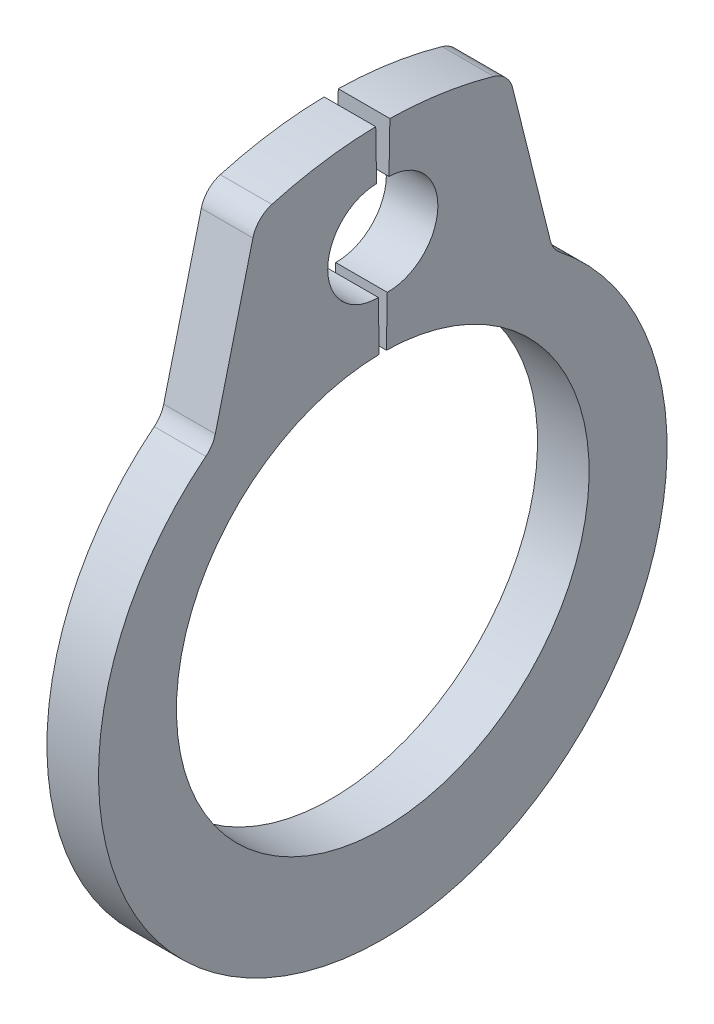
SolidWorks part; units mm, degrees
material "Cast Carbon Steel"
ref_plane "Front" through (0, 0, 0) normal (0, 0, 1) x (1, 0, 0)
ref_plane "Top" through (0, 0, 0) normal (0, 1, 0) x (1, 0, 0)
ref_plane "Right" through (0, 0, 0) normal (1, 0, 0) x (0, 0, -1)
sketch "Sketch1" plane through (0, 0, 0) normal (1, 0, 0) x (0, 0, -1)
  line L0 (0, 0) -> (0, 2.8) construction
  line L1 (-0.0489, 2.7996) -> (-0.096, 5.4992) construction
  line L2 (-0.096, 5.4992) -> (-1.651, 5.472) construction
  line L3 (-1.651, 5.472) -> (-2.3042, 2.8522) construction
  line L4 (0.096, 5.4992) -> (0.0489, 2.7996) construction
  line L5 (0.096, 5.4992) -> (1.651, 5.472) construction
  line L6 (1.651, 5.472) -> (2.3042, 2.8522) construction
  line L7 (-2.3042, 2.8522) -> (-1.7596, 2.1781) construction
  line L8 (2.3042, 2.8522) -> (1.7596, 2.1781) construction
  line L9 (0, -2.8) -> (0, -4.1) construction
  line L10 (-1.651, 5.472) -> (-0.0489, 2.7996) construction
  line L11 (0.0489, 2.7996) -> (0.0606, 3.4745)
  line L12 (0, 2.8) -> (0, 5.5) construction
  line L13 (1.7122, 5.2267) -> (2.3042, 2.8522)
  line L14 (-1.7122, 5.2267) -> (-2.3042, 2.8522)
  line L16 (0.0842, 4.8243) -> (0.096, 5.4992)
  line L17 (-0.0842, 4.8243) -> (-0.096, 5.4992)
  line L18 (-0.0606, 3.4745) -> (-0.0489, 2.7996)
  circle A0 centre (0, 0) radius 2.8 construction
  arc A1 (-0.0489, 2.7996) -> (0.0489, 2.7996) centre (0, 0) ccw
  circle A2 centre (0, -0.242) radius 3.858 construction
  arc A3 (0.0842, 4.8243) -> (0.0606, 3.4745) centre (0.0724, 4.1494) cw
  arc A4 (-0.0606, 3.4745) -> (-0.0842, 4.8243) centre (-0.0724, 4.1494) cw
  arc A6 (-2.3042, 2.8522) -> (2.3042, 2.8522) centre (0, -0.242) ccw
  arc A7 (0.096, 5.4992) -> (1.7122, 5.2267) centre (0, 0) cw
  arc A8 (-0.096, 5.4992) -> (-1.7122, 5.2267) centre (0, 0) ccw
  dimension "A" = 5.6
  dimension "Smin" = 0.8667
  dimension "D1" = 75
  dimension "Angle" = 1
  dimension "H" = 2.7
  dimension "D2" = 1.35
extrude "Extrude1" add sketch "Sketch1" along normal mid plane 0.7
fillet "Fillet1" radius 0.37 4 edges at (0, 2.8522, 2.3042) (0, 5.2267, 1.7122) (0, 5.2267, -1.7122) (0, 2.8522, -2.3042)
sketch "Sketch2" plane through (0, 0, 0) normal (0, 0, 1) x (1, 0, 0)
  line L0 (-2, 0) -> (6, 0)
  line L1 (6, 0) -> (6, -3)
  line L2 (-0.4, -3) -> (-1.85, -3)
  line L3 (6, -3) -> (0.4, -3)
  line L4 (0.4, -3) -> (0.4, -2.85)
  line L5 (0.4, -2.85) -> (-0.4, -2.85)
  line L6 (-0.4, -2.85) -> (-0.4, -3)
  line L7 (-0.4, -3) -> (-2, -3) construction
  line L8 (-2, -3) -> (-2, 0) construction
  line L9 (0, -2.85) -> (0, 0) construction
  line L10 (6, 0) -> (14.0551, 0) construction
  line L11 (-1.85, -3) -> (-2, -2.85)
  line L12 (-2, -2.85) -> (-2, 0)
  dimension "D2" = 8
  dimension "D3" = 2
  dimension "D1" = 45
revolve "Revolve1" [suppressed] add sketch "Sketch2" angle 360 about L10
equation "\"D2@Sketch2\" = \"W@Sketch2\"*10"
equation "\"D3@Sketch2\" = \"D2@Sketch2\"/4"
equation "\"Smin@Sketch1\" = \"Smax@Sketch1\"/1.5"
equation "\"D2@Sketch1\" = \"H@Sketch1\"/2"
